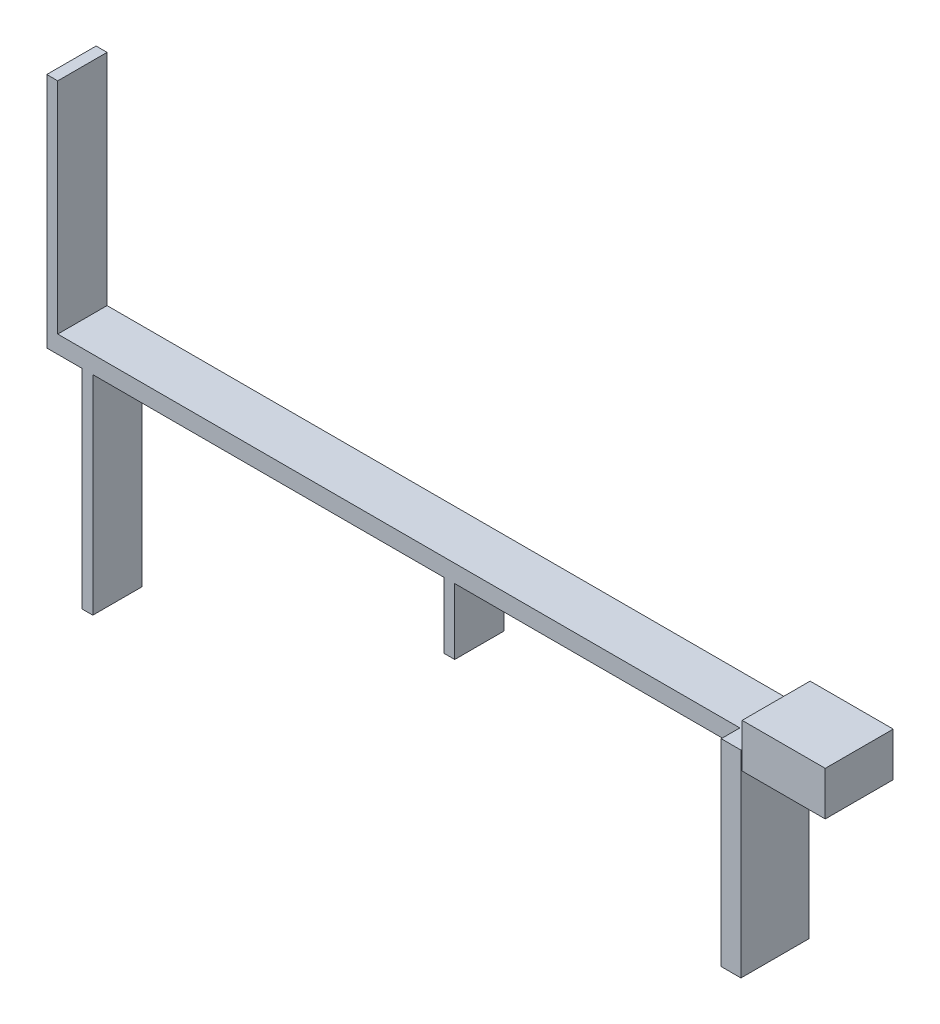
SolidWorks part; units mm, degrees
ref_plane "Front Plane" through (0, 0, 0) normal (0, 0, 1) x (1, 0, 0)
ref_plane "Top Plane" through (0, 0, 0) normal (0, 1, 0) x (1, 0, 0)
ref_plane "Right Plane" through (0, 0, 0) normal (1, 0, 0) x (0, 0, -1)
sketch "Sketch1" plane through (0, 0, 0) normal (0, 0, 1) x (1, 0, 0)
  line L0 (-5877.01, 8443.2) -> (-5877.01, 21864.2) construction
  line L1 (3302.8587, 36497.6944) -> (-4277.01, 36497.6944)
  line L2 (3302.8587, 36497.6944) -> (3302.8587, 32497.6944)
  line L3 (3302.8587, 32497.6944) -> (-4277.01, 32497.6944)
  line L4 (-4277.01, 36497.6944) -> (-4277.01, 32497.6944)
  line L5 (-4277.01, 34497.6944) -> (-68802.8275, 34497.6944)
  line L6 (-4277.01, 34497.6944) -> (-4277.01, 32497.6944)
  line L7 (-4277.01, 32497.6944) -> (-68802.8275, 32497.6944)
  line L8 (-68802.8275, 34497.6944) -> (-68802.8275, 32497.6944)
  line L9 (-68802.8275, 34497.6944) -> (-67802.8275, 34497.6944)
  line L10 (-68802.8275, 34497.6944) -> (-68802.8275, 60401.4469)
  line L11 (-68802.8275, 60401.4469) -> (-67802.8275, 60401.4469)
  line L12 (-67802.8275, 34497.6944) -> (-67802.8275, 60401.4469)
  line L13 (-33279, 32497.6944) -> (-32279, 32497.6944)
  line L14 (-33279, 32497.6944) -> (-33279, 26237.307)
  line L15 (-33279, 26237.307) -> (-32279, 26237.307)
  line L16 (-32279, 32497.6944) -> (-32279, 26237.307)
  line L17 (-65243.9957, 32497.6944) -> (-66243.9957, 32497.6944)
  line L18 (-65243.9957, 32497.6944) -> (-65243.9957, 19793.5368)
  line L19 (-65243.9957, 19793.5368) -> (-66243.9957, 19793.5368)
  line L20 (-66243.9957, 32497.6944) -> (-66243.9957, 19793.5368)
  line L21 (-4277.01, 32497.6944) -> (-5877.01, 32497.6944)
  line L22 (-4277.01, 32497.6944) -> (-4277.01, 16582.4275)
  line L23 (-4277.01, 16582.4275) -> (-5877.01, 16582.4275)
  line L24 (-5877.01, 32497.6944) -> (-5877.01, 16582.4275)
  dimension "D1" = 2000
  dimension "D2" = 4000
  dimension "D3" = 1600
  dimension "D4" = 1000
  dimension "D5" = 1000
  dimension "D6" = 1200
  dimension "D7" = 1200
  dimension "D8" = 1000
extrude "Extrude1" add sketch "Sketch1" along normal blind 6200 contours L1 L4 L3 L2
sketch "Sketch2" plane through (0, 0, 0) normal (0, 0, -1) x (-1, 0, 0)
  line L1 (4383.6974, 16097.6944) -> (6183.6974, 16097.6944)
  line L2 (4383.6974, 16097.6944) -> (4383.6974, 34097.6944)
  line L3 (4383.6974, 34097.6944) -> (6183.6974, 34097.6944)
  line L4 (6183.6974, 16097.6944) -> (6183.6974, 34097.6944)
  line L7 (-3302.8587, 32497.6944) -> (4277.01, 32497.6944) construction
  dimension "D1" = 1800
  dimension "D2" = 1600
  dimension "D3" = 18000
extrude "Extrude2" add sketch "Sketch2" against normal blind 6200
sketch "Sketch3" plane through (0, 0, 0) normal (0, 0, 1) x (1, 0, 0)
  line L1 (-6183.6974, 34097.6944) -> (-69383.6974, 34097.6944)
  line L2 (-6183.6974, 34097.6944) -> (-6183.6974, 32497.6944)
  line L3 (-6183.6974, 32497.6944) -> (-69383.6974, 32497.6944)
  line L4 (-69383.6974, 34097.6944) -> (-69383.6974, 32497.6944)
  line L5 (-69383.6974, 34097.6944) -> (-68383.6974, 34097.6944)
  line L6 (-69383.6974, 34097.6944) -> (-69383.6974, 54097.6944)
  line L7 (-69383.6974, 54097.6944) -> (-68383.6974, 54097.6944)
  line L8 (-68383.6974, 34097.6944) -> (-68383.6974, 54097.6944)
  line L9 (-33183.6974, 32497.6944) -> (-32183.6974, 32497.6944)
  line L10 (-33183.6974, 32497.6944) -> (-33183.6974, 26497.6944)
  line L11 (-33183.6974, 26497.6944) -> (-32183.6974, 26497.6944)
  line L12 (-32183.6974, 32497.6944) -> (-32183.6974, 26497.6944)
  line L13 (-65183.6974, 32497.6944) -> (-66183.6974, 32497.6944)
  line L14 (-65183.6974, 32497.6944) -> (-65183.6974, 13497.6944)
  line L15 (-65183.6974, 13497.6944) -> (-66183.6974, 13497.6944)
  line L16 (-66183.6974, 32497.6944) -> (-66183.6974, 13497.6944)
  line L17 (3302.8587, 32497.6944) -> (-4277.01, 32497.6944) construction
  line L19 (-6183.6974, 16097.6944) -> (-6183.6974, 34097.6944) construction
  dimension "D1" = 1000
  dimension "D2" = 6000
  dimension "D3" = 1000
  dimension "D4" = 19000
  dimension "D5" = 1000
  dimension "D6" = 20000
  dimension "D7" = 1600
  dimension "D8" = 59000
  dimension "D9" = 63200
  dimension "D10" = 26000
extrude "Extrude3" add sketch "Sketch3" along normal blind 4500 contours L1 L2 L3 L4 | L12 L11 L10 L9 | L5 L8 L7 L6 | L14 L15 L16 L13
